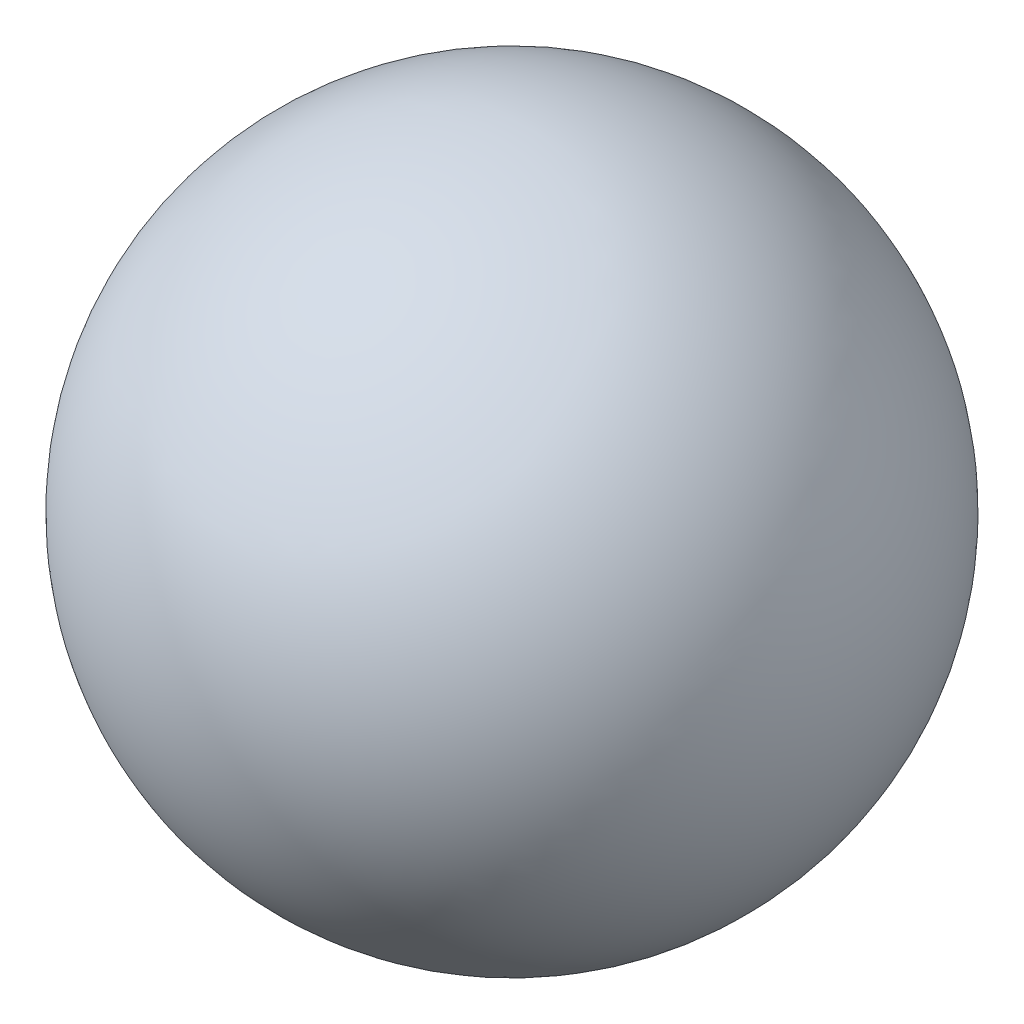
SolidWorks part; units mm, degrees
ref_plane "前视基准面" through (0, 0, 0) normal (0, 0, 1) x (1, 0, 0)
ref_plane "上视基准面" through (0, 0, 0) normal (0, 1, 0) x (1, 0, 0)
ref_plane "右视基准面" through (0, 0, 0) normal (1, 0, 0) x (0, 0, -1)
sketch "草图1" plane through (0, 0, 0) normal (0, 1, 0) x (1, 0, 0)
  line L0 (0, 6.9361) -> (0, -4.0328) construction
  circle A0 centre (0, 0) radius 1
  point P5 (0, 6.9361)
  point P6 (0, -4.0328)
  dimension "D1" = 2
revolve "旋转2" add sketch "草图1" angle 360 about L0
